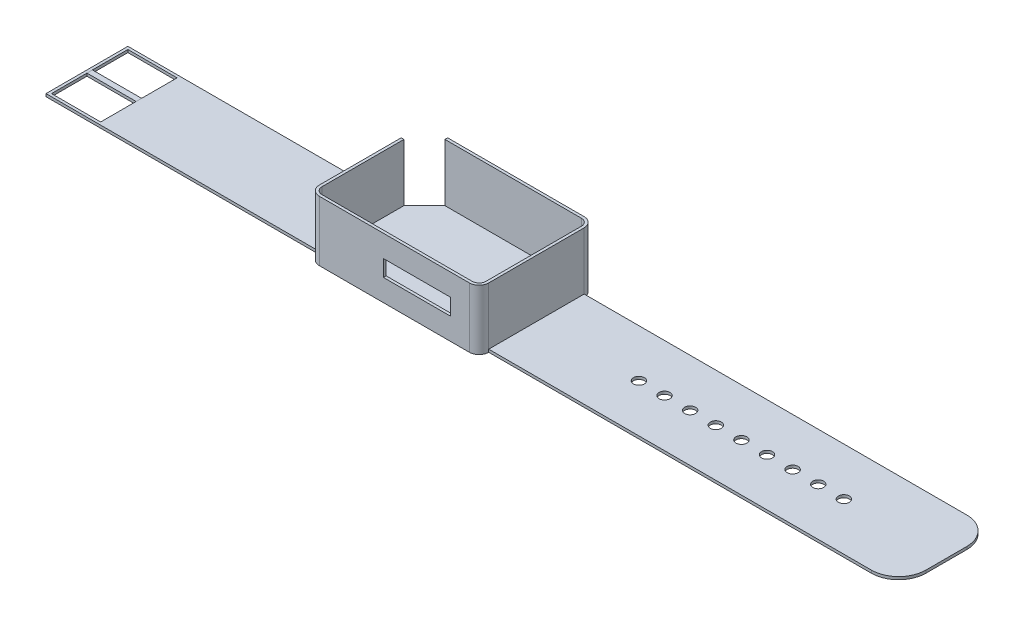
SolidWorks part; units mm, degrees
ref_plane "Front Plane" through (0, 0, 0) normal (0, 0, 1) x (1, 0, 0)
ref_plane "Top Plane" through (0, 0, 0) normal (0, 1, 0) x (1, 0, 0)
ref_plane "Right Plane" through (0, 0, 0) normal (1, 0, 0) x (0, 0, -1)
sketch "Sketch1" plane through (0, 0, 0) normal (0, 1, 0) x (1, 0, 0)
  line L0 (-38.692, 22.1485) -> (10.2724, 22.1485)
  line L1 (-46.192, 14.6485) -> (-46.192, -14.316)
  line L2 (13.808, 18.613) -> (13.808, -14.316)
  line L3 (-42.6565, -17.8515) -> (10.2724, -17.8515)
  line L4 (-16.192, 22.1485) -> (-16.192, 23.1485)
  line L5 (-16.192, 23.1485) -> (11.2724, 23.1485)
  line L6 (-16.192, 22.1485) -> (-38.692, 22.1485) construction
  line L7 (-31.192, 22.1485) -> (-38.692, 22.1485) construction
  line L8 (-38.692, 22.1485) -> (-46.192, 14.6485)
  line L9 (-16.192, 23.1485) -> (-38.692, 23.1485)
  line L10 (14.808, 19.613) -> (14.808, -14.316)
  line L11 (-38.692, 23.1485) -> (-38.692, 22.1485)
  line L12 (-47.192, 14.6485) -> (-47.192, -15.316)
  line L13 (14.808, -14.316) -> (14.808, -15.316)
  line L14 (-16.192, -17.8515) -> (-16.192, -18.8515)
  line L15 (-16.192, -18.8515) -> (11.2724, -18.8515)
  line L16 (-47.192, 14.6485) -> (-46.192, 14.6485)
  line L17 (-16.192, -18.8515) -> (-43.6565, -18.8515)
  arc A0 (13.808, 18.613) -> (10.2724, 22.1485) centre (10.2724, 18.613) ccw
  arc A1 (-46.192, -14.316) -> (-42.6565, -17.8515) centre (-42.6565, -14.316) ccw
  arc A2 (10.2724, -17.8515) -> (13.808, -14.316) centre (10.2724, -14.316) ccw
  arc A3 (14.808, 19.613) -> (11.2724, 23.1485) centre (11.2724, 19.613) ccw
  arc A4 (-47.192, -15.316) -> (-43.6565, -18.8515) centre (-43.6565, -15.316) ccw
  arc A5 (11.2724, -18.8515) -> (14.808, -15.316) centre (11.2724, -15.316) ccw
extrude "Boss-Extrude1" add sketch "Sketch1" along normal blind 22 contours L9 L11 L0 L4 | L15 A5 L13 L10 A3 L5 L4 L0 A0 L2 A2 L3 L14 | L12 A4 L17 L14 L3 A1 L1 L16 | L3 A2 L2 A0 L0 L8 L1 A1
shell "Shell1" thickness 1
sketch "Sketch2" plane through (0, 22, 0) normal (0, 1, 0) x (1, 0, 0)
  line L0 (-38.692, 22.1485) -> (-37.692, 22.1485)
  line L1 (-46.192, 14.6485) -> (-46.192, 13.6485)
  line L2 (-46.192, 13.6485) -> (-45.7778, 13.6485)
  line L3 (-45.7778, 13.6485) -> (-37.692, 21.7343)
  line L4 (-37.692, 21.7343) -> (-45.7778, 13.6485) construction
  line L5 (-37.692, 21.7343) -> (-45.7778, 13.6485) construction
  line L6 (-37.692, 21.7343) -> (-37.692, 22.1485)
  line L7 (-38.692, 22.1485) -> (-46.192, 14.6485)
extrude "Cut-Extrude1" cut sketch "Sketch2" against normal blind 21
sketch3d "3DSketch2"
  line L4 (-47.192, 1.0003, -14.6485) -> (-47.192, 1.0003, 15.316)
  line L5 (-47.192, 22, -14.6485) -> (-47.192, 0, -14.6485) construction
  line L6 (-47.192, 22, 15.316) -> (-47.192, 0, 15.316) construction
  line L7 (-47.192, 1.0003, 15.316) -> (-47.192, 0, 15.316)
  line L8 (-47.192, 0, 15.316) -> (-47.192, 0, -14.6485)
  line L9 (-47.192, 1.0003, -14.6485) -> (-47.192, 0, -14.6485)
extrude "Boss-Extrude2" add sketch "3DSketch2" along direction (1, 0, 0) on the side of the normal blind 100
sketch "Sketch3" plane through (14.808, 0, 0) normal (1, 0, 0) x (0, 0, -1)
  line L0 (-15.316, 0) -> (-15.316, 1)
  line L1 (-15.316, 22) -> (-15.316, 0) construction
  line L2 (-15.316, 1) -> (19.613, 1)
  line L3 (19.613, 22) -> (19.613, 0) construction
  line L4 (19.613, 1) -> (19.613, 0)
  line L5 (19.613, 0) -> (-15.316, 0)
extrude "Boss-Extrude3" add sketch "Sketch3" along normal blind 150
sketch "Sketch4" plane through (0, 0, 18.8515) normal (0, 0, 1) x (1, 0, 0)
  line L0 (-43.6565, 22) -> (11.2724, 22) construction
  line L1 (-16.192, 22) -> (-16.192, 0) construction
  line L2 (-43.6565, 0) -> (11.2724, 0) construction
  line L3 (-16.192, 11) -> (11.2724, 11) construction
  line L4 (11.2724, 22) -> (11.2724, 0) construction
  line L5 (-2.4598, 11) -> (11.2724, 11) construction
  line L6 (4.4063, 11) -> (4.4063, 14)
  line L7 (4.4063, 11) -> (4.4063, 8)
  line L8 (4.4063, 8) -> (-16.192, 8)
  line L9 (4.4063, 14) -> (-16.192, 14)
  line L10 (-16.192, 14) -> (-20.192, 14)
  line L11 (-16.192, 8) -> (-20.192, 8)
  line L12 (-20.192, 14) -> (-20.192, 8)
extrude "Cut-Extrude2" cut sketch "Sketch4" against normal blind 10
sketch "Sketch5" plane through (0, 1.0003, 0) normal (0, 1, 0) x (1, 0, 0)
  line L0 (14.808, 2.1485) -> (164.808, 2.1485) construction
  line L1 (14.808, 19.613) -> (14.808, -15.316) construction
  line L2 (164.808, 19.613) -> (164.808, -15.316) construction
  line L3 (89.808, 2.1485) -> (164.808, 2.1485) construction
  line L4 (89.808, 2.1485) -> (14.808, 2.1485) construction
  line L5 (52.308, 2.1485) -> (89.808, 2.1485) construction
  line L6 (89.808, 2.1485) -> (127.308, 2.1485) construction
  line L7 (108.558, 2.1485) -> (127.308, 2.1485) construction
  line L8 (108.558, 2.1485) -> (89.808, 2.1485) construction
  line L9 (71.058, 2.1485) -> (52.308, 2.1485) construction
  line L10 (71.058, 2.1485) -> (89.808, 2.1485) construction
  line L11 (52.308, 2.1485) -> (71.058, 2.1485) construction
  line L12 (71.058, 2.1485) -> (89.808, 2.1485) construction
  line L13 (89.808, 2.1485) -> (108.558, 2.1485) construction
  line L14 (108.558, 2.1485) -> (127.308, 2.1485) construction
  line L15 (108.558, 2.1485) -> (89.808, 2.1485) construction
  line L16 (89.808, 2.1485) -> (71.058, 2.1485) construction
  circle A0 centre (127.308, 2.1485) radius 2.0046
  circle A1 centre (108.558, 2.1485) radius 2
  circle A2 centre (89.808, 2.1485) radius 2
  circle A3 centre (71.058, 2.1485) radius 2
  circle A4 centre (52.308, 2.1485) radius 2
  circle A5 centre (61.683, 2.1485) radius 2
  circle A6 centre (117.933, 2.1485) radius 2
  circle A7 centre (99.183, 2.1485) radius 2
  circle A8 centre (80.433, 2.1485) radius 2
extrude "Cut-Extrude3" cut sketch "Sketch5" against normal blind 10
fillet "Fillet1" radius 10 1 edges at (164.808, 0.5, -19.613)
fillet "Fillet2" radius 10 1 edges at (164.808, 0.5, 15.316)
sketch "Sketch6" plane through (0, 1.0003, 0) normal (0, 1, 0) x (1, 0, 0)
  line L0 (-147.192, 14.6485) -> (-137.192, 14.6485) construction
  line L1 (-47.192, 14.6485) -> (-147.192, 14.6485) construction
  line L2 (-137.192, 14.6485) -> (-127.192, 14.6485) construction
  line L4 (-47.192, -15.316) -> (-147.192, -15.316) construction
  line L5 (-127.192, -15.316) -> (-147.192, -15.316) construction
  line L6 (-147.192, -15.316) -> (-147.192, 14.6485) construction
  line L8 (-137.192, 13.6485) -> (-128.192, 13.6485)
  line L9 (-137.192, 13.6485) -> (-146.192, 13.6485)
  line L11 (-146.192, 13.6485) -> (-146.192, -14.316)
  line L12 (-137.192, -15.316) -> (-137.192, -14.316) construction
  line L13 (-146.192, -14.316) -> (-128.192, -14.316)
  line L15 (-128.192, 13.6485) -> (-128.192, -14.316)
extrude "Cut-Extrude4" cut sketch "Sketch6" against normal blind 10
sketch "Sketch7" plane through (-128.192, 0, 0) normal (-1, 0, 0) x (0, 0, 1)
  line L0 (-13.6485, 1.0003) -> (14.316, 1.0003) construction
  line L1 (14.316, 1.0003) -> (-13.6485, 1.0003) construction
  line L2 (0.3337, 1.0003) -> (0.3337, 0) construction
  line L3 (14.316, 0) -> (-13.6485, 0) construction
  line L4 (0.3337, 0.5001) -> (1.3337, 0.5001) construction
  line L5 (0.3337, 0.5001) -> (-0.6663, 0.5001) construction
  line L6 (1.3337, 0.5001) -> (1.3337, 1.0003)
  line L7 (1.3337, 0.5001) -> (1.3337, 0)
  line L8 (1.3337, 0) -> (-0.6663, 0)
  line L9 (-0.6663, 0) -> (-0.6663, 1.0003)
  line L10 (-0.6663, 1.0003) -> (1.3337, 1.0003)
extrude "Boss-Extrude5" add sketch "Sketch7" along normal blind 18 separate body
